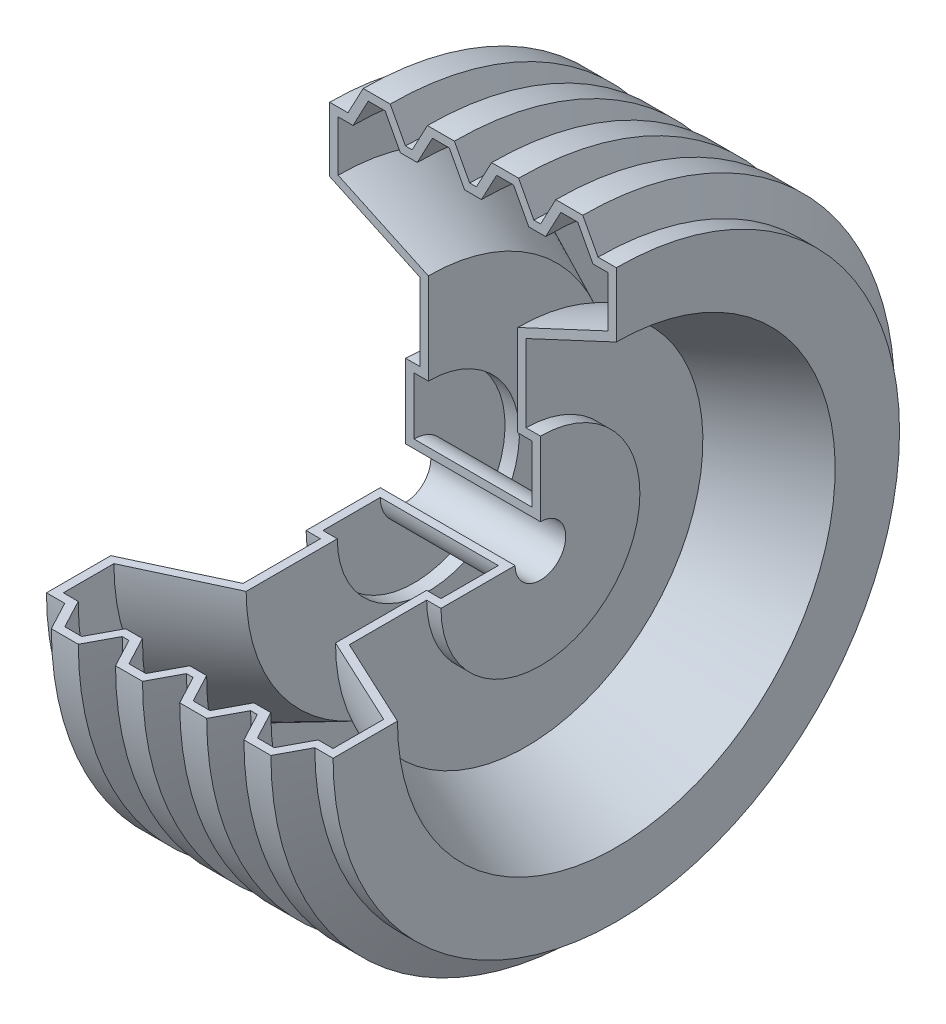
SolidWorks part; units mm, degrees
material "Copper"
ref_plane "Front Plane" through (0, 0, 0) normal (0, 0, 1) x (1, 0, 0)
ref_plane "Top Plane" through (0, 0, 0) normal (0, 1, 0) x (1, 0, 0)
ref_plane "Right Plane" through (0, 0, 0) normal (1, 0, 0) x (0, 0, -1)
sketch "Sketch2" plane through (0, 0, 0) normal (0, 0, 1) x (1, 0, 0)
  line L0 (0, -137.9962) -> (0, 221.7835) construction
  line L1 (-156.9249, 0) -> (163.0309, 0) construction
  line L2 (-35, 20) -> (35, 20)
  line L3 (35, 20) -> (35, 54)
  line L4 (35, 54) -> (26.5, 54)
  line L5 (26.5, 54) -> (26.5, 108.0525)
  line L6 (26.5, 108.0525) -> (80, 133)
  line L7 (80, 133) -> (80, 163)
  line L8 (80, 163) -> (71.1562, 163)
  line L9 (71.1562, 163) -> (62.1172, 180)
  line L10 (62.1172, 180) -> (52.1172, 180)
  line L11 (52.1172, 180) -> (43.0781, 163)
  line L12 (43.0781, 163) -> (33.0781, 163)
  line L13 (33.0781, 163) -> (24.0391, 180)
  line L14 (24.0391, 180) -> (14.0391, 180)
  line L15 (14.0391, 180) -> (5, 163)
  line L16 (5, 163) -> (-5, 163)
  line L17 (-14.0391, 180) -> (-5, 163)
  line L18 (-24.0391, 180) -> (-14.0391, 180)
  line L19 (-33.0781, 163) -> (-24.0391, 180)
  line L20 (-43.0781, 163) -> (-33.0781, 163)
  line L21 (-52.1172, 180) -> (-43.0781, 163)
  line L22 (-62.1172, 180) -> (-52.1172, 180)
  line L23 (-71.1562, 163) -> (-62.1172, 180)
  line L24 (-80, 163) -> (-71.1562, 163)
  line L25 (-80, 133) -> (-80, 163)
  line L26 (-26.5, 108.0525) -> (-80, 133)
  line L27 (-26.5, 54) -> (-26.5, 108.0525)
  line L28 (-35, 54) -> (-26.5, 54)
  line L29 (-35, 20) -> (-35, 54)
  point P7 (0, 0)
  point P22 (0, 0)
  point P23 (0, 0)
  point P24 (0, 0)
  point P25 (0, 0)
  point P26 (0, 221.7835)
  point P28 (13.2626, 180)
  point P29 (21.6044, 180)
  point P30 (0, 163)
  point P43 (0, 20)
  dimension "D1" = 40
  dimension "D2" = 108
  dimension "D3" = 30
  dimension "D4" = 360
  dimension "D5" = 10
  dimension "D6" = 10
  dimension "D7" = 10
  dimension "D8" = 10
  dimension "D9" = 62
  dimension "D10" = 62
  dimension "D11" = 62
  dimension "D12" = 62
  dimension "D13" = 17
  dimension "D14" = 160
  dimension "D15" = 65
  dimension "D16" = 53
  dimension "D17" = 70
revolve "Revolve-Thin1" add sketch "Sketch2" angle 270 about L1
